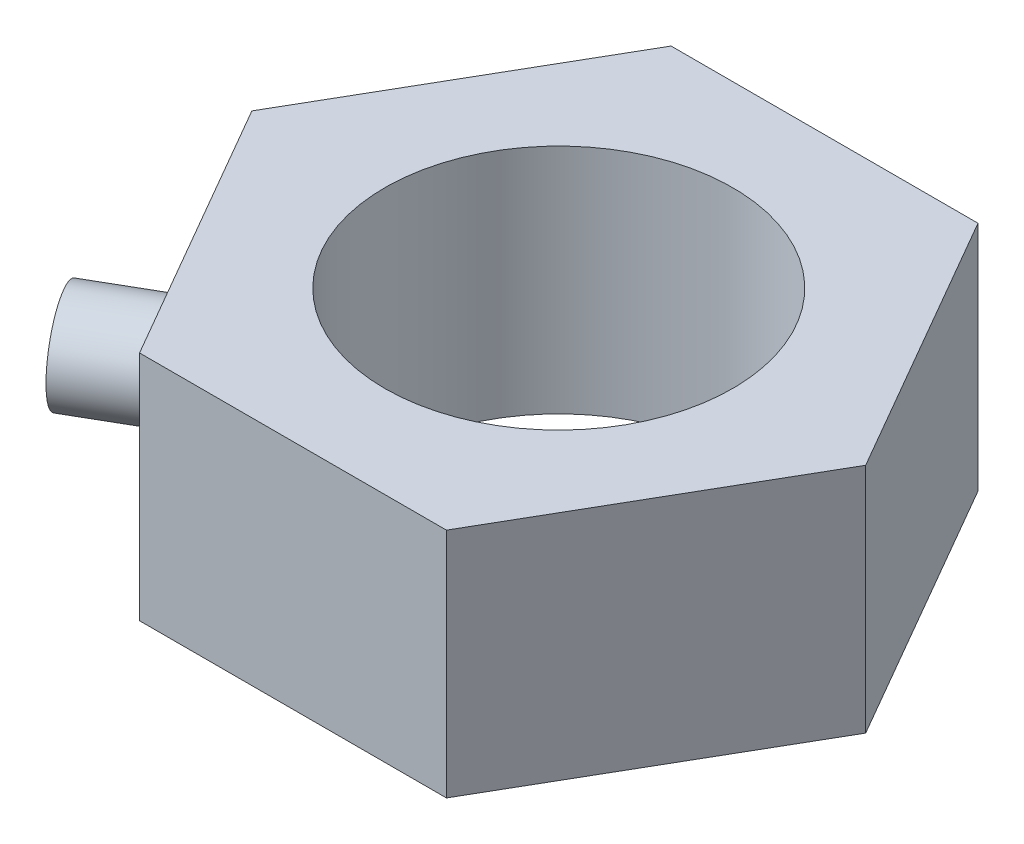
SolidWorks part; units mm, degrees
ref_plane "Piano frontale" through (0, 0, 0) normal (0, 0, 1) x (1, 0, 0)
ref_plane "Piano superiore" through (0, 0, 0) normal (0, 1, 0) x (1, 0, 0)
ref_plane "Piano destro" through (0, 0, 0) normal (1, 0, 0) x (0, 0, -1)
sketch "Schizzo2" plane through (0, 0, 0) normal (0, 1, 0) x (1, 0, 0)
  line L1 (3.1754, 0) -> (1.5877, 2.75)
  line L2 (1.5877, 2.75) -> (-1.5877, 2.75)
  line L3 (-1.5877, 2.75) -> (-3.1754, 0)
  line L4 (-3.1754, 0) -> (-1.5877, -2.75)
  line L5 (-1.5877, -2.75) -> (1.5877, -2.75)
  line L6 (1.5877, -2.75) -> (3.1754, 0)
  circle A0 centre (0, 0) radius 2.75
  point P1 (0, 0)
  dimension "D1" = 5.5
extrude "Estrusione-Estrusione3" add sketch "Schizzo2" along normal mid plane 2.4 contours L2 L3 L4 L5 L6 L1
sketch "Schizzo3" plane through (0, 1.2, 0) normal (0, 1, 0) x (1, 0, 0)
  circle A0 centre (0, 0) radius 1.8
  dimension "D1" = 3.6
extrude "Taglio-Estrusione1" cut sketch "Schizzo3" against normal mid plane 100 contours A0
sketch "Schizzo4" plane through (-2.3816, 0, 1.375) normal (-0.866, 0, 0.5) x (0.5, 0, 0.866)
  circle A0 centre (0, 0) radius 0.5
  dimension "D1" = 1
extrude "Estrusione-Estrusione4" add sketch "Schizzo4" along normal blind 1
